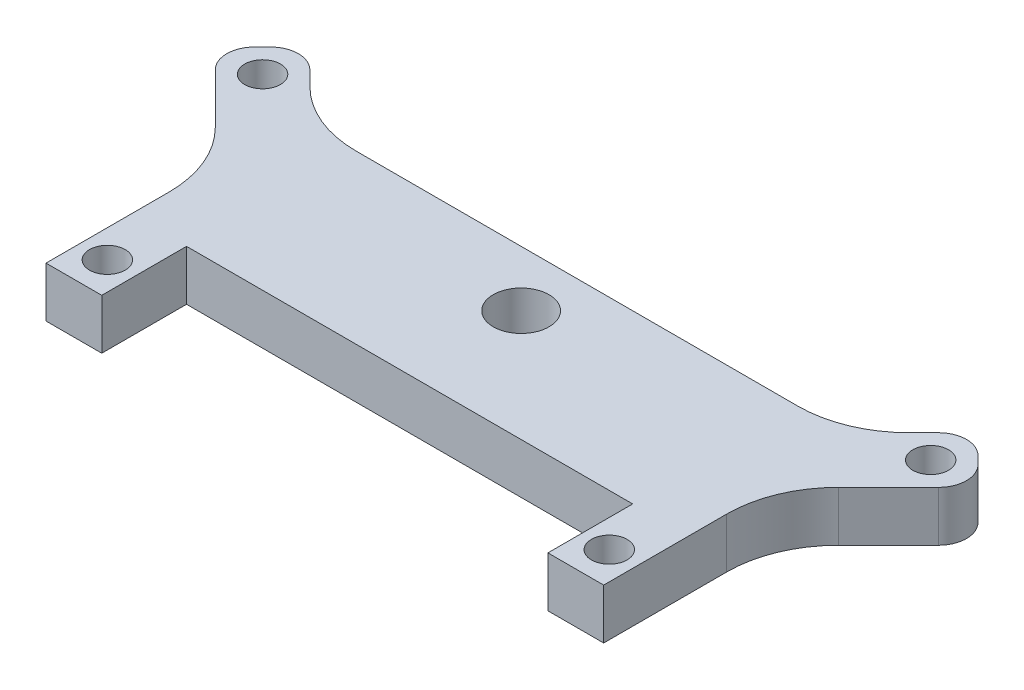
SolidWorks part; units mm, degrees
material "PLA"
ref_plane "Front Plane" through (0, 0, 0) normal (0, 0, 1) x (1, 0, 0)
ref_plane "Top Plane" through (0, 0, 0) normal (0, 1, 0) x (1, 0, 0)
ref_plane "Right Plane" through (0, 0, 0) normal (1, 0, 0) x (0, 0, -1)
sketch "Sketch1" plane through (0, 0, 0) normal (0, 1, 0) x (1, 0, 0)
  line L0 (-20, 0) -> (20, 0)
  line L1 (20, 0) -> (20, -7.6)
  line L2 (20, -7.6) -> (25, -7.6)
  line L3 (25, -7.6) -> (25, 7.5754)
  line L4 (25, 7.5754) -> (34.1924, 16.7678)
  line L5 (34.1924, 16.7678) -> (29.9497, 21.0104)
  line L6 (29.9497, 21.0104) -> (23.9393, 15)
  line L7 (23.9393, 15) -> (-23.9393, 15)
  line L8 (-23.9393, 15) -> (-29.9497, 21.0104)
  line L9 (-29.9497, 21.0104) -> (-34.1924, 16.7678)
  line L10 (-34.1924, 16.7678) -> (-25, 7.5754)
  line L11 (-25, 7.5754) -> (-25, -7.6)
  line L12 (-25, -7.6) -> (-20, -7.6)
  line L13 (-20, -7.6) -> (-20, 0)
  line L14 (29.9497, 16.7678) -> (32.0711, 18.8891) construction
  line L15 (-29.9497, 16.7678) -> (-32.0711, 18.8891) construction
  circle A0 centre (-22.5, -4.6) radius 1.6
  circle A1 centre (22.5, -4.6) radius 1.6
  circle A2 centre (-29.9497, 16.7678) radius 1.6
  circle A3 centre (29.9497, 16.7678) radius 1.6
  circle A4 centre (0, 10) radius 2.5
  point P19 (0, 0)
  point P21 (22.5, -7.6)
  point P23 (-22.5, -7.6)
  point P33 (0, 15)
  dimension "D1" = 3.2
  dimension "D2" = 3.2
  dimension "D13" = 3.2
  dimension "D14" = 3.2
  dimension "D17" = 5
  dimension "D3" = 45
  dimension "D4" = 5
  dimension "D5" = 5
  dimension "D6" = 3
  dimension "D7" = 4.6
  dimension "D8" = 21.3678
  dimension "D9" = 6
  dimension "D10" = 6
  dimension "D11" = 15
  dimension "D12" = 135
  dimension "D15" = 3
  dimension "D16" = 13
  dimension "D18" = 5
extrude "Boss-Extrude1" add sketch "Sketch1" along normal blind 4.5
fillet "Fillet1" radius 10 4 edges at (-25, 2.25, -7.5754) (25, 2.25, -7.5754) (23.9393, 2.25, -15) (-23.9393, 2.25, -15)
fillet "Fillet2" radius 2.5 4 edges at (-34.1924, 2.25, -16.7678) (-29.9497, 2.25, -21.0104) (29.9497, 2.25, -21.0104) (34.1924, 2.25, -16.7678)
